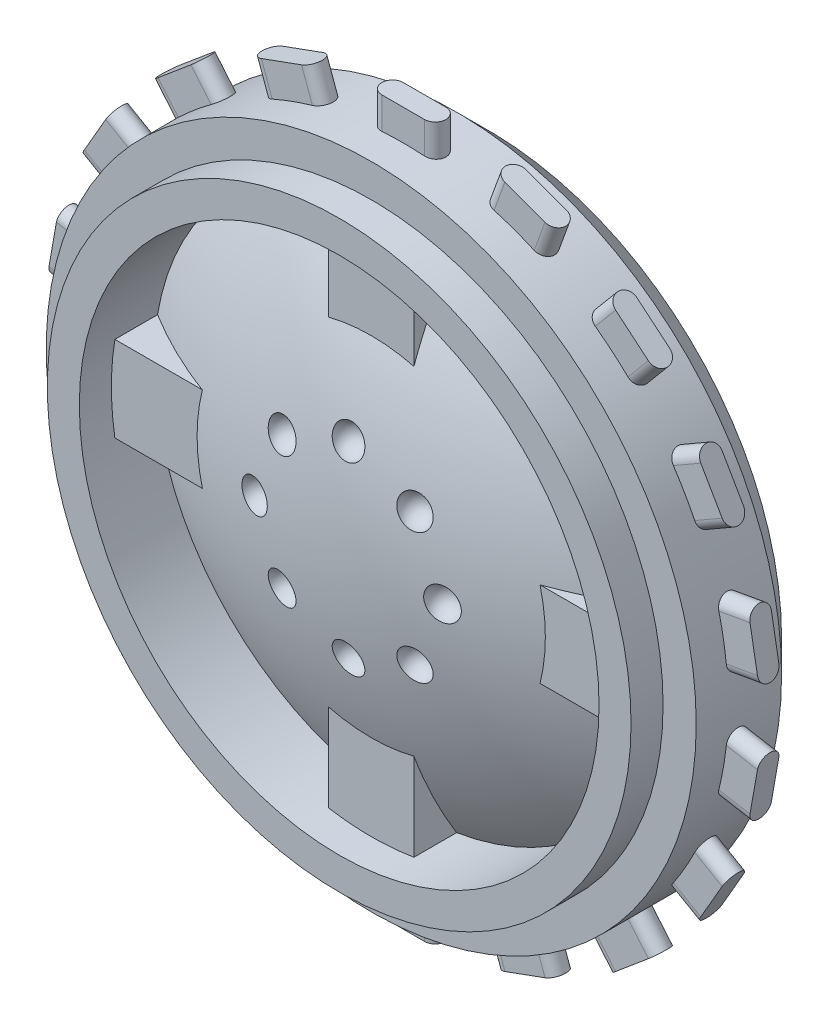
SolidWorks part; units mm, degrees
material "AISI 1035 Steel (SS)"
ref_plane "Front Plane" through (0, 0, 0) normal (0, 0, 1) x (1, 0, 0)
ref_plane "Top Plane" through (0, 0, 0) normal (0, 1, 0) x (1, 0, 0)
ref_plane "Right Plane" through (0, 0, 0) normal (1, 0, 0) x (0, 0, -1)
sketch "Sketch1" plane through (0, 0, 0) normal (1, 0, 0) x (0, 0, -1)
  line L0 (-5.6464, 0) -> (0.8077, 0)
  line L1 (5.6464, 4.8387) -> (5.6464, 22.1412)
  line L2 (3.2258, 24.5618) -> (-3.2258, 24.5618)
  line L4 (0.8077, 4.8387) -> (5.6464, 4.8387)
  line L5 (0.8077, 0) -> (0.8077, 4.8387)
  line L6 (3.2258, 24.5618) -> (5.6464, 22.1412)
  line L7 (-5.6464, 22.0574) -> (-3.2258, 22.0574)
  line L8 (-3.2258, 22.0574) -> (-3.2258, 24.5618)
  line L9 (-5.6464, 22.0574) -> (-5.6464, 19.6393)
  line L10 (-5.6464, 19.6393) -> (-0.0004, 19.6393)
  arc A1 (-0.0004, 19.6393) -> (-5.6464, 0) centre (31.3334, 0) ccw
revolve "Revolve1" add sketch "Sketch1" angle 360 about L0
ref_plane "Plane1" through (0, 22.0574, 0) normal (0, 1, 0) x (1, 0, 0)
sketch "Sketch3" plane through (0, 22.0574, 0) normal (0, 1, 0) x (1, 0, 0)
  line L0 (-1.6129, 0.8077) -> (1.6129, 0.8077)
  line L1 (-1.6129, -0.8077) -> (1.6129, -0.8077)
  line L2 (4.8387, 5.6464) -> (-4.8387, 5.6464) construction
  arc A0 (-1.6129, 0.8077) -> (-1.6129, -0.8077) centre (-1.6129, 0) ccw
  arc A1 (1.6129, -0.8077) -> (1.6129, 0.8077) centre (1.6129, 0) ccw
  dimension "D1" = 3.2258
  dimension "D2" = 5.6464
extrude "Boss-Extrude1" add sketch "Sketch3" along normal blind 4.8412
pattern_circular "CirPattern1" count 18 every 20 about axis through (0, 0, 0) along (0, 0, 1) of "Boss-Extrude1"
sketch "Sketch4" plane through (0, 0, 3.2258) normal (0, 0, 1) x (1, 0, 0)
  line L0 (-3.2258, 3.2258) -> (-3.2258, 20.4582)
  line L1 (-3.2258, -20.4582) -> (3.2258, -20.4582)
  line L2 (-3.2258, -20.4582) -> (-3.2258, -3.2258)
  line L3 (-3.2258, 20.4582) -> (3.2258, 20.4582)
  line L4 (3.2258, -20.4582) -> (3.2258, -3.2258)
  line L5 (3.2258, 3.2258) -> (20.6231, 3.2258)
  line L6 (3.2258, 3.2258) -> (3.2258, 20.4582)
  line L7 (-20.6231, -3.2258) -> (-3.2258, -3.2258)
  line L8 (-20.6231, -3.2258) -> (-20.6231, 3.2258)
  line L9 (-20.6231, 3.2258) -> (-3.2258, 3.2258)
  line L10 (20.6231, -3.2258) -> (20.6231, 3.2258)
  line L11 (3.2258, -3.2258) -> (20.6231, -3.2258)
  point P0 (0, 0)
  point P6 (0, 0)
extrude "Boss-Extrude2" add sketch "Sketch4" against normal blind 3.4392
ref_plane "Plane2" through (0, 0, 4.9632) normal (0, 0, 1) x (1, 0, 0)
sketch "Sketch5" plane through (0, 0, 4.9632) normal (0, 0, 1) x (1, 0, 0)
  line L0 (-1.2141, 7.1044) -> (1.2141, 7.1044)
  arc A0 (1.2141, 7.1044) -> (-1.2141, 7.1044) centre (0, 7.1044) ccw
  dimension "D1" = 7.1044
revolve "Cut-Revolve1" cut sketch "Sketch5" angle 360 about L0
pattern_circular "CirPattern2" count 8 every 45 about axis through (0, 0, 0) along (0, 0, 1) of "Cut-Revolve1"
